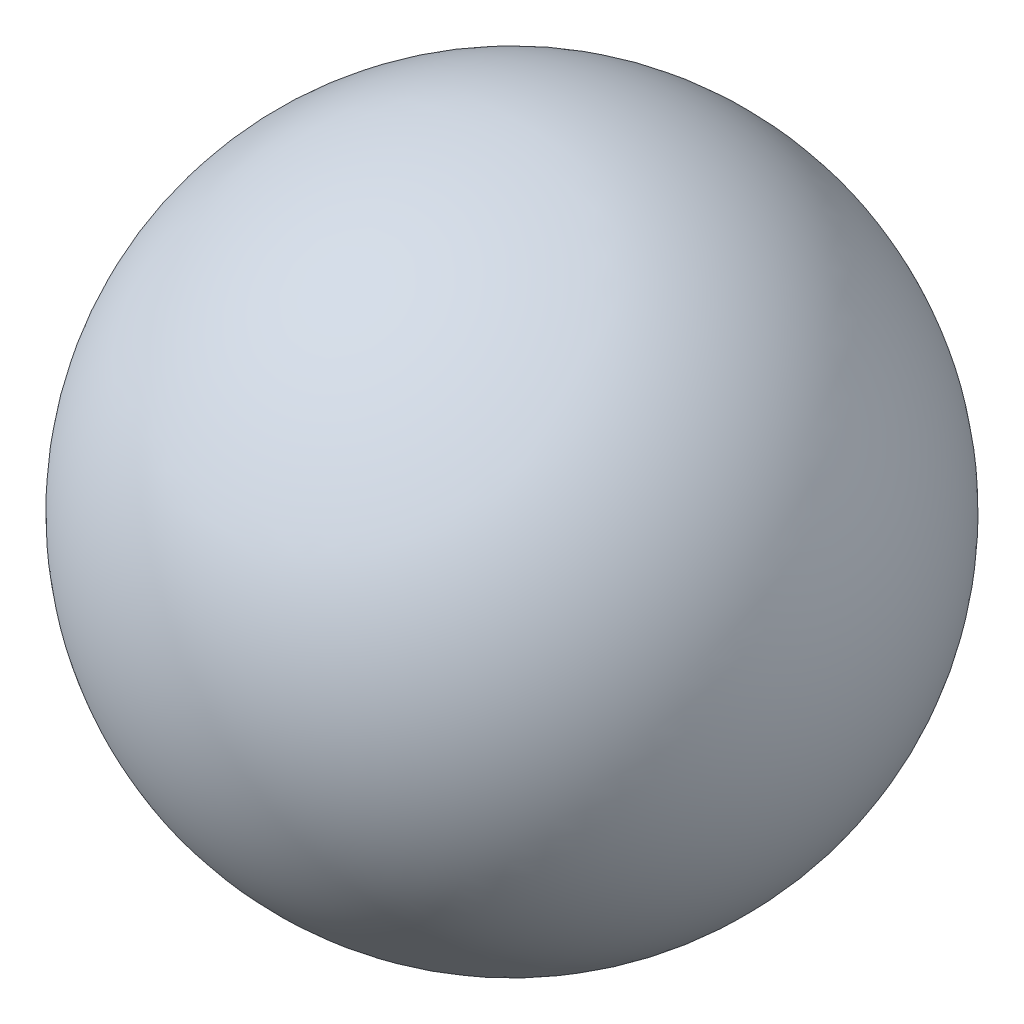
SolidWorks part; units mm, degrees
ref_plane "前视基准面" through (0, 0, 0) normal (0, 0, 1) x (1, 0, 0)
ref_plane "上视基准面" through (0, 0, 0) normal (0, 1, 0) x (1, 0, 0)
ref_plane "右视基准面" through (0, 0, 0) normal (1, 0, 0) x (0, 0, -1)
sketch "草图1" plane through (0, 0, 0) normal (0, 1, 0) x (1, 0, 0)
  line L0 (0, 6.9361) -> (0, -4.0328) construction
  circle A0 centre (0, 0) radius 2.5
  dimension "D1" = 5
revolve "旋转2" add sketch "草图1" angle 360 about L0
